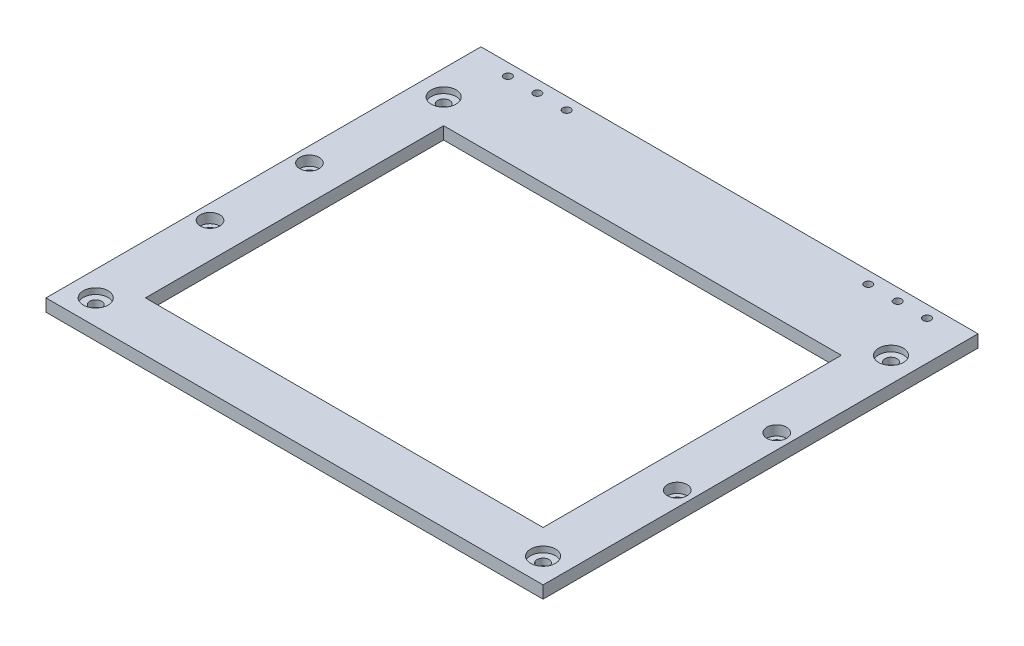
SolidWorks part; units mm, degrees
ref_plane "Front Plane" through (0, 0, 0) normal (0, 0, 1) x (1, 0, 0)
ref_plane "Top Plane" through (0, 0, 0) normal (0, 1, 0) x (1, 0, 0)
ref_plane "Right Plane" through (0, 0, 0) normal (1, 0, 0) x (0, 0, -1)
sketch "Sketch1" plane through (0, 0, 0) normal (0, 1, 0) x (1, 0, 0)
  line L1 (0, 0) -> (254, 0)
  line L2 (0, 0) -> (0, 203.2)
  line L3 (0, 203.2) -> (254, 203.2)
  line L4 (254, 0) -> (254, 203.2)
  line L5 (12.7, 190.5) -> (241.3, 190.5) construction
  line L6 (12.7, 190.5) -> (12.7, 12.7) construction
  line L7 (25.4, 177.8) -> (228.6, 177.8)
  line L8 (25.4, 177.8) -> (25.4, 25.4)
  line L9 (25.4, 25.4) -> (228.6, 25.4)
  line L10 (228.6, 177.8) -> (228.6, 25.4)
  line L11 (12.7, 12.7) -> (241.3, 12.7) construction
  line L12 (241.3, 190.5) -> (241.3, 12.7) construction
  circle A0 centre (12.7, 190.5) radius 3.05
  circle A1 centre (241.3, 190.5) radius 3.05
  circle A2 centre (241.3, 12.7) radius 3.05
  circle A3 centre (12.7, 12.7) radius 3.05
  dimension "D11" = 6.1
  dimension "D12" = 6.1
  dimension "D13" = 6.1
  dimension "D14" = 6.1
  dimension "D1" = 254
  dimension "D2" = 203.2
  dimension "D3" = 25.4
  dimension "D4" = 25.4
  dimension "D5" = 25.4
  dimension "D6" = 25.4
  dimension "D7" = 12.7
  dimension "D8" = 12.7
  dimension "D9" = 12.7
  dimension "D10" = 12.7
extrude "Boss-Extrude1" add sketch "Sketch1" along normal blind 6.35
sketch "Sketch2" plane through (0, 6.35, 0) normal (0, 1, 0) x (1, 0, 0)
  circle A0 centre (12.7, 190.5) radius 6.35
  circle A1 centre (241.3, 190.5) radius 6.35
  circle A2 centre (241.3, 12.7) radius 6.35
  circle A3 centre (12.7, 12.7) radius 6.35
  dimension "D1" = 12.7
  dimension "D2" = 12.7
  dimension "D3" = 12.7
  dimension "D4" = 12.7
extrude "Cut-Extrude1" cut sketch "Sketch2" against normal blind 3
hole_wizard "CBORE for M5 SHCS1" positions "Sketch3" profile "Sketch4" counterbore size "M5" standard "ANSI Metric" end condition through all
sketch "Sketch3" plane through (0, 6.35, 0) normal (0, 1, 0) x (1, 0, 0)
  line L0 (254, 0) -> (254, 203.2) construction
  line L1 (0, 0) -> (254, 0) construction
  line L2 (254, 203.2) -> (0, 203.2) construction
  line L3 (0, 203.2) -> (0, 0) construction
  point P0 (246.38, 76.2)
  point P2 (246.38, 127)
  point P4 (7.62, 76.2)
  point P6 (7.62, 127)
  dimension "D1" = 7.62
  dimension "D2" = 76.2
  dimension "D3" = 76.2
  dimension "D4" = 7.62
  dimension "D5" = 76.2
  dimension "D6" = 76.2
  dimension "D7" = 7.62
  dimension "D8" = 7.62
  dimension "D9" = 50.8
sketch "Sketch4" plane through (246.38, 6.35, -76.2) normal (1, 0, 0) x (0, 0, 1)
  line L0 (0, 0) -> (0, 6.35)
  line L1 (0, 6.35) -> (2.75, 6.35)
  line L3 (2.75, 6.35) -> (2.75, 5)
  line L4 (2.75, 5) -> (5, 5)
  line L5 (5, 5) -> (5, 0)
  line L7 (5, 0) -> (0, 0)
  line L11 (0, -6.35) -> (0, 107.95) construction
  dimension "Thru Hole Dia." = 5.5
  dimension "Thru Hole Depth" = 6.35
  dimension "C'Bore Dia." = 10
  dimension "C'Bore Depth" = 5
sketch "Sketch5" plane through (0, 0, 0) normal (0, -1, 0) x (1, 0, 0)
  line L1 (254, -203.2) -> (0, -203.2)
  line L2 (254, -203.2) -> (254, -222.25)
  line L3 (254, -222.25) -> (0, -222.25)
  line L4 (0, -203.2) -> (0, -222.25)
  dimension "D1" = 19.05
extrude "Boss-Extrude3" add sketch "Sketch5" against normal blind 6.35
sketch "Sketch6" plane through (0, 6.35, 0) normal (0, 1, 0) x (1, 0, 0)
  line L0 (0, 222.25) -> (254, 222.25) construction
  line L1 (12.7, 222.25) -> (57.15, 222.25) construction
  line L2 (12.7, 222.25) -> (12.7, 209.55) construction
  line L3 (12.7, 209.55) -> (57.15, 209.55) construction
  line L4 (57.15, 222.25) -> (57.15, 209.55) construction
  line L5 (12.925, 223.1204) -> (50012.925, 223.1204) construction
  line L10 (0, 222.25) -> (0, 0) construction
  line L12 (12.925, 210.1204) -> (56.925, 210.1204) construction
  line L13 (12.925, 210.1204) -> (12.925, 242.1204) construction
  line L14 (12.925, 242.1204) -> (56.925, 242.1204) construction
  line L15 (56.925, 210.1204) -> (56.925, 242.1204) construction
  line L19 (127, 222.25) -> (127, -49777.75) construction
  line L20 (228.6, 177.8) -> (25.4, 177.8) construction
  line L21 (12.925, 216.1204) -> (50012.925, 216.1204) construction
  line L22 (34.925, 242.1204) -> (34.925, -49757.8796) construction
  line L23 (49.925, 242.1204) -> (49.925, -49757.8796) construction
  line L24 (19.925, 242.1204) -> (19.925, -49757.8796) construction
  line L25 (197.075, 210.1204) -> (197.075, 242.1204) construction
  line L26 (241.075, 242.1204) -> (197.075, 242.1204) construction
  line L27 (241.075, 210.1204) -> (241.075, 242.1204) construction
  line L28 (241.075, 210.1204) -> (197.075, 210.1204) construction
  line L29 (196.85, 222.25) -> (196.85, 209.55) construction
  line L30 (241.3, 209.55) -> (196.85, 209.55) construction
  line L31 (241.3, 222.25) -> (241.3, 209.55) construction
  line L32 (241.3, 222.25) -> (196.85, 222.25) construction
  line L33 (12.925, 236.1204) -> (50012.925, 236.1204) construction
  line L34 (12.925, 229.1204) -> (50012.925, 229.1204) construction
  line L35 (219.075, 216.1204) -> (219.075, 50216.1204) construction
  line L36 (234.075, 216.1204) -> (234.075, 50216.1204) construction
  line L37 (204.0632, 216.1204) -> (204.0632, 50216.1204) construction
  circle A0 centre (19.925, 216.1204) radius 2
  circle A1 centre (34.925, 216.1204) radius 2
  circle A2 centre (49.9368, 216.1204) radius 2
  circle A3 centre (204.0632, 216.1204) radius 2
  circle A4 centre (219.075, 216.1204) radius 2
  circle A5 centre (234.075, 216.1204) radius 2
  point P10 (56.925, 226.1204)
  point P24 (127, 222.25)
  point P27 (127, 177.8)
  point P29 (34.925, 242.1204)
  point P30 (34.925, 210.1204)
  point P62 (219.075, 242.1204)
  dimension "D11" = 4
  dimension "D12" = 4
  dimension "D13" = 4
  dimension "D1" = 44.45
  dimension "D2" = 13
  dimension "D3" = 10
  dimension "D4" = 12.7
  dimension "D5" = 12.7
  dimension "D6" = 15
  dimension "D7" = 32
  dimension "D8" = 44
  dimension "D9" = 0.225
  dimension "D10" = 15
  dimension "D14" = 20
  dimension "D15" = 13
extrude "Cut-Extrude2" cut sketch "Sketch6" against normal blind 4.5
sketch "Sketch7" plane through (0, 1.85, 0) normal (0, 1, 0) x (1, 0, 0)
  circle A0 centre (19.925, 216.1204) radius 1.75
  circle A1 centre (34.925, 216.1204) radius 1.75
  circle A2 centre (49.9368, 216.1204) radius 1.75
  circle A3 centre (204.0632, 216.1204) radius 1.75
  circle A4 centre (219.075, 216.1204) radius 1.75
  circle A5 centre (234.075, 216.1204) radius 1.75
  dimension "D1" = 3.5
  dimension "D2" = 3.5
  dimension "D3" = 3.5
  dimension "D4" = 3.5
  dimension "D5" = 3.5
  dimension "D6" = 3.5
extrude "Cut-Extrude3" cut sketch "Sketch7" against normal blind 4.5
